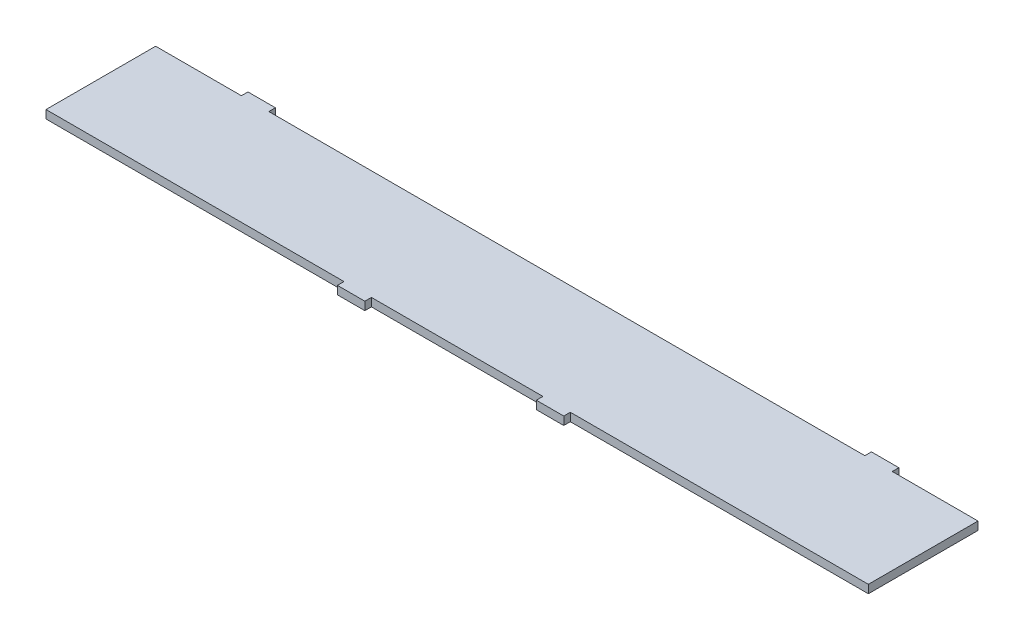
SolidWorks part; units mm, degrees
ref_plane "Alzado" through (0, 0, 0) normal (0, 0, 1) x (1, 0, 0)
ref_plane "Planta" through (0, 0, 0) normal (0, 1, 0) x (1, 0, 0)
ref_plane "Vista lateral" through (0, 0, 0) normal (1, 0, 0) x (0, 0, -1)
sketch "Croquis1" plane through (0, 0, 0) normal (0, 1, 0) x (1, 0, 0)
  line L1 (-750, -100) -> (750, -100)
  line L2 (-750, -100) -> (-750, 100)
  line L3 (-750, 100) -> (750, 100)
  line L4 (750, -100) -> (750, 100)
  line L5 (-750, -100) -> (750, 100) construction
  line L6 (-750, 100) -> (750, -100) construction
  point P0 (0, 0)
  dimension "D1" = 1500
  dimension "D2" = 200
extrude "Saliente-Extruir1" add sketch "Croquis1" along normal blind 15
sketch "Croquis3" plane through (0, 0, 0) normal (0, 1, 0) x (1, 0, 0)
  line L0 (750, 100) -> (-750, 100) construction
  line L1 (-400, 100) -> (-350, 100) construction
  line L2 (-400, 100) -> (-400, 115) construction
  line L3 (-400, 115) -> (-350, 115) construction
  line L4 (-350, 100) -> (-350, 115) construction
  line L5 (0, 0) -> (0, 251.2938) construction
  line L6 (0, 0) -> (-750, 0) construction
  line L7 (-750, 100) -> (-750, -100) construction
  line L20 (543.59, 112) -> (593.59, 112)
  line L21 (-543.59, 100) -> (-593.59, 100)
  line L22 (-543.59, 100) -> (-543.59, 112)
  line L23 (-543.59, 112) -> (-593.59, 112)
  line L24 (-593.59, 100) -> (-593.59, 112)
  line L25 (543.59, 100) -> (543.59, 112)
  line L26 (543.59, 100) -> (593.59, 100)
  line L27 (593.59, 100) -> (593.59, 112)
  line L28 (-750, -100) -> (750, -100) construction
  line L29 (-206.41, -100) -> (-156.41, -100)
  line L30 (-206.41, -100) -> (-206.41, -112)
  line L31 (-206.41, -112) -> (-156.41, -112)
  line L32 (-156.41, -100) -> (-156.41, -112)
  line L33 (206.41, -100) -> (206.41, -112)
  line L34 (156.41, -100) -> (156.41, -112)
  line L35 (206.41, -100) -> (156.41, -100)
  line L36 (206.41, -112) -> (156.41, -112)
  point P9 (-375, 100)
  dimension "D1" = 15
  dimension "D2" = 50
  dimension "D3" = 375
  dimension "D4" = 143.59
  dimension "D5" = 50
  dimension "D6" = 12
  dimension "D7" = 12
  dimension "D8" = 50
  dimension "D9" = 143.59
extrude "Saliente-Extruir2" add sketch "Croquis3" along normal blind 15
